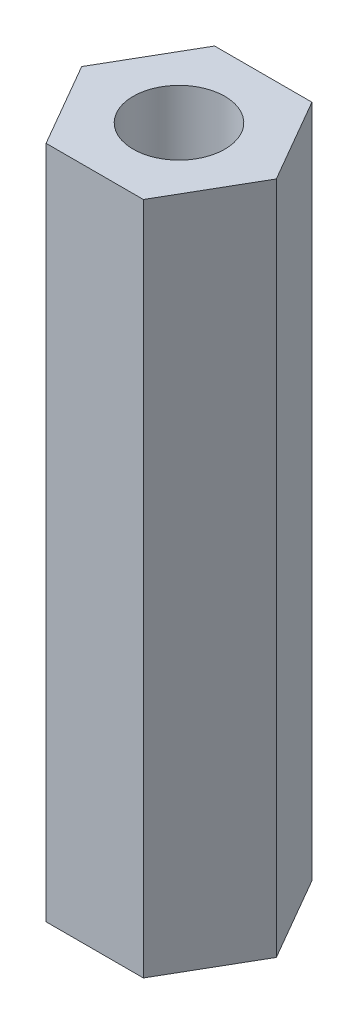
SolidWorks part; units mm, degrees
ref_plane "Front Plane" through (0, 0, 0) normal (0, 0, 1) x (1, 0, 0)
ref_plane "Top Plane" through (0, 0, 0) normal (0, 1, 0) x (1, 0, 0)
ref_plane "Right Plane" through (0, 0, 0) normal (1, 0, 0) x (0, 0, -1)
sketch "Sketch1" plane through (0, 0, 0) normal (0, 1, 0) x (1, 0, 0)
  line L1 (3.6662, 0) -> (1.8331, 3.175)
  line L2 (1.8331, 3.175) -> (-1.8331, 3.175)
  line L3 (-1.8331, 3.175) -> (-3.6662, 0)
  line L4 (-3.6662, 0) -> (-1.8331, -3.175)
  line L5 (-1.8331, -3.175) -> (1.8331, -3.175)
  line L6 (1.8331, -3.175) -> (3.6662, 0)
  circle A0 centre (0, 0) radius 3.175 construction
  dimension "D1" = 6.35
extrude "Boss-Extrude1" add sketch "Sketch1" along normal blind 25.4
hole_wizard "#8-32 Tapped Hole1" positions "Sketch3" profile "Sketch2" tap size "#8-32" standard "ANSI Inch" end condition through all
sketch "Sketch3" plane through (0, 0, 0) normal (0, -1, 0) x (-1, 0, 0)
  point P0 (0, 0)
sketch "Sketch2" plane through (0, 0, 0) normal (1, 0, 0) x (0, 0, -1)
  line L0 (0, 0) -> (0, 25.4)
  line L1 (0, 25.4) -> (1.7272, 25.4)
  line L2 (1.7272, 25.4) -> (1.7272, 0)
  line L5 (1.7272, 0) -> (0, 0)
  line L11 (0, -6.35) -> (0, 107.95) construction
  dimension "Thru Tap Drill Dia." = 3.4544
  dimension "Thru Tap Drill Depth" = 25.4
cosmetic thread "Hole Thread1"
